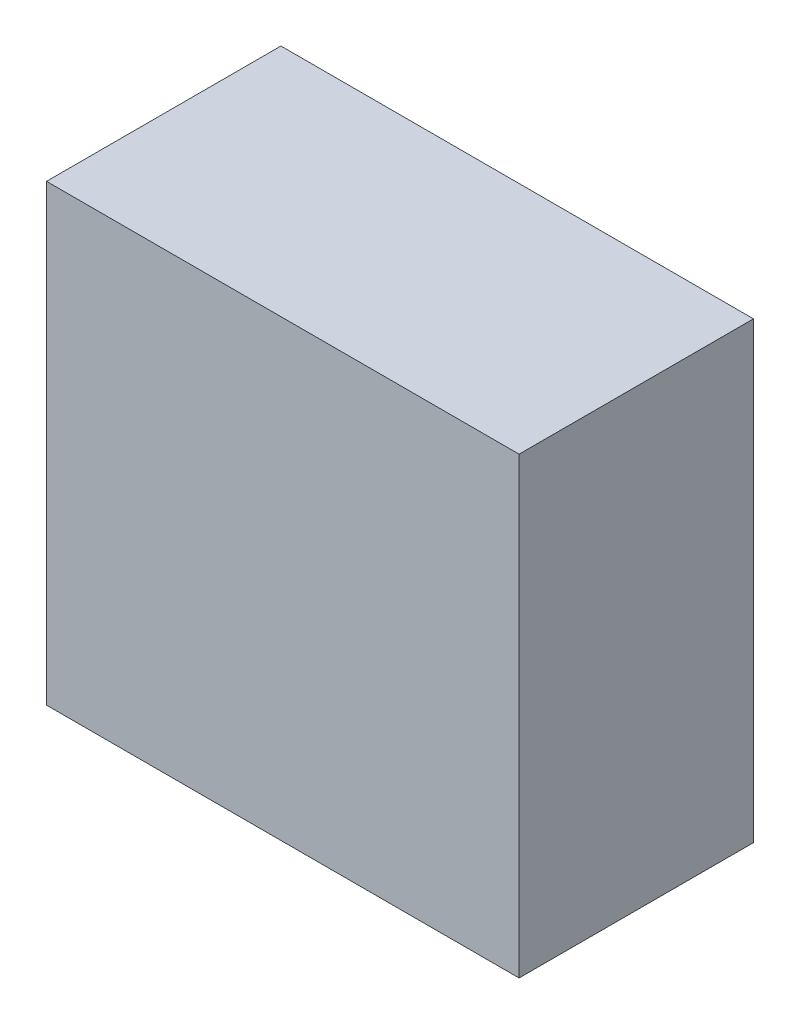
SolidWorks part; units mm, degrees
ref_plane "Front Plane" through (0, 0, 0) normal (0, 0, 1) x (1, 0, 0)
ref_plane "Top Plane" through (0, 0, 0) normal (0, 1, 0) x (1, 0, 0)
ref_plane "Right Plane" through (0, 0, 0) normal (1, 0, 0) x (0, 0, -1)
sketch "Sketch1" plane through (0, 0, 0) normal (0, 1, 0) x (1, 0, 0)
  line L1 (0, 0) -> (3.175, 0)
  line L2 (0, 0) -> (0, 1.5748)
  line L3 (0, 1.5748) -> (3.175, 1.5748)
  line L4 (3.175, 0) -> (3.175, 1.5748)
  dimension "D1" = 1.5748
  dimension "D2" = 3.175
extrude "Boss-Extrude1" add sketch "Sketch1" along normal blind 3.048
